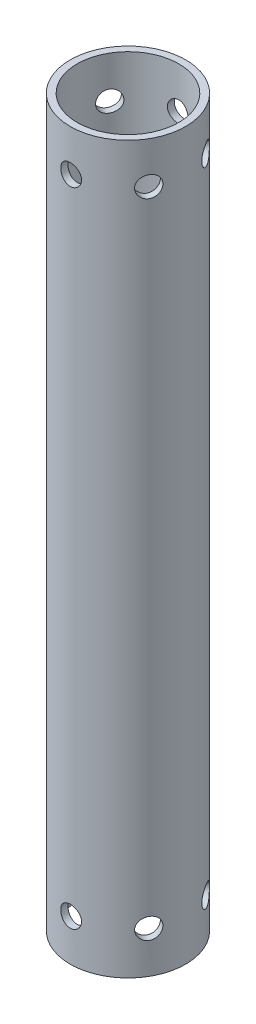
SolidWorks part; units mm, degrees
material "6061-T6 (SS)"
ref_plane "Front Plane" through (0, 0, 0) normal (0, 0, 1) x (1, 0, 0)
ref_plane "Top Plane" through (0, 0, 0) normal (0, 1, 0) x (1, 0, 0)
ref_plane "Right Plane" through (0, 0, 0) normal (1, 0, 0) x (0, 0, -1)
sketch "Sketch1" plane through (0, 0, 0) normal (0, 1, 0) x (1, 0, 0)
  circle A0 centre (0, 0) radius 34.925
  circle A1 centre (0, 0) radius 39.6875
  dimension "D1" = 69.85
  dimension "D2" = 4.7625
extrude "Boss-Extrude1" add sketch "Sketch1" along normal blind 498.602
ref_plane "Plane1" through (0, 0, 39.6875) normal (0, 0, 1) x (1, 0, 0)
hole_wizard "9/16 (0.5625) Diameter Hole1" positions "Sketch6" profile "Sketch7" hole size "9/16" standard "ANSI Inch"
sketch "Sketch6" plane through (0, 0, 39.6875) normal (0, 0, 1) x (1, 0, 0)
  line L0 (0, 0) -> (0, 28.575) construction
  line L1 (0, 28.575) -> (0, 470.027) construction
  line L4 (34.925, 498.602) -> (-34.925, 498.602) construction
  point P2 (0, 28.575)
  point P4 (0, 470.027)
  dimension "D1" = 28.575
  dimension "D2" = 28.575
sketch "Sketch7" plane through (0, 470.027, 39.6875) normal (1, 0, 0) x (0, -1, 0)
  line L0 (0, 0) -> (0, 4.7625)
  line L1 (0, 4.7625) -> (7.1437, 4.7625)
  line L2 (7.1437, 4.7625) -> (7.1437, 0)
  line L5 (7.1437, 0) -> (0, 0)
  line L11 (0, -6.35) -> (0, 107.95) construction
  dimension "Thru Hole Dia." = 14.2875
  dimension "Thru Hole Depth" = 4.7625
pattern_circular "CirPattern1" count 6 over 360 about axis through (0, 498.602, 0) along (0, -1, 0) of "9/16 (0.5625) Diameter Hole1"
ref_plane "Plane2" through (-39.6875, 0, 0) normal (-1, 0, 0) x (0, 0, 1)
